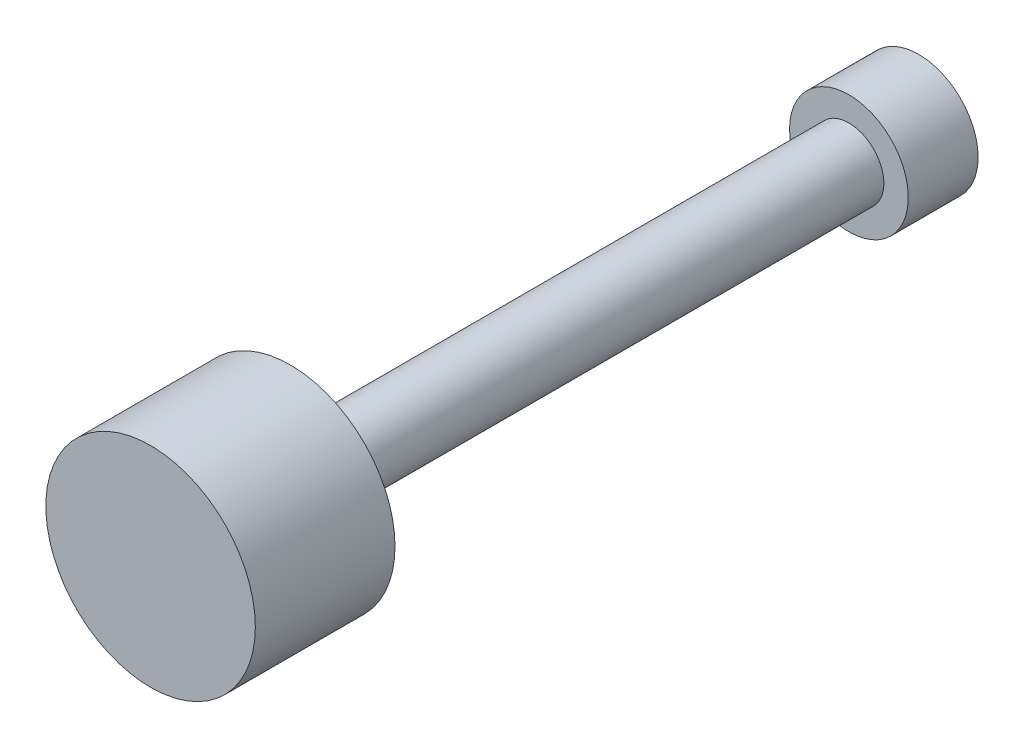
SolidWorks part; units mm, degrees
ref_plane "Front Plane" through (0, 0, 0) normal (0, 0, 1) x (1, 0, 0)
ref_plane "Top Plane" through (0, 0, 0) normal (0, 1, 0) x (1, 0, 0)
ref_plane "Right Plane" through (0, 0, 0) normal (1, 0, 0) x (0, 0, -1)
sketch "Sketch2" plane through (0, 0, 0) normal (0, 0, 1) x (1, 0, 0)
  circle A0 centre (0, 0) radius 50
extrude "Boss-Extrude1" add sketch "Sketch2" along normal blind 1000
sketch "Sketch3" plane through (0, 0, 1000) normal (0, 0, 1) x (1, 0, 0)
  circle A0 centre (0, 0) radius 150
extrude "Boss-Extrude2" add sketch "Sketch3" against normal blind 200
sketch "Sketch4" plane through (0, 0, 0) normal (0, 0, -1) x (-1, 0, 0)
  circle A0 centre (0, 0) radius 85
extrude "Boss-Extrude3" add sketch "Sketch4" along normal blind 100
